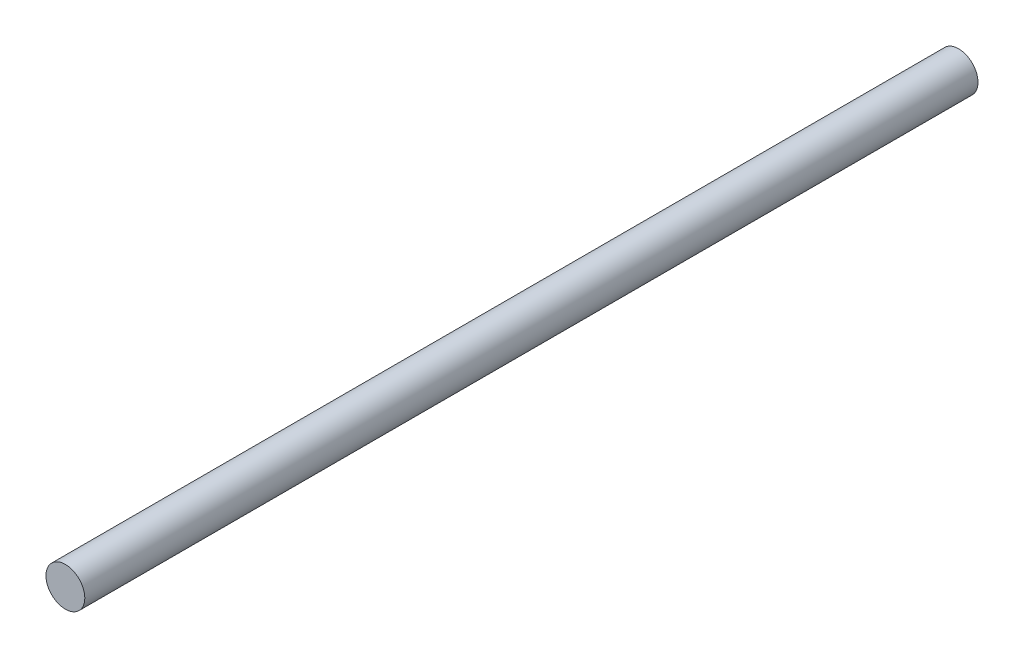
SolidWorks part; units mm, degrees
ref_plane "Piano frontale" through (0, 0, 0) normal (0, 0, 1) x (1, 0, 0)
ref_plane "Piano superiore" through (0, 0, 0) normal (0, 1, 0) x (1, 0, 0)
ref_plane "Piano destro" through (0, 0, 0) normal (1, 0, 0) x (0, 0, -1)
sketch "Schizzo1" plane through (0, 0, 0) normal (0, 0, 1) x (1, 0, 0)
  circle A0 centre (0, 0) radius 5
  dimension "D1" = 10
extrude "Estrusione-Estrusione1" add sketch "Schizzo1" along normal blind 230
